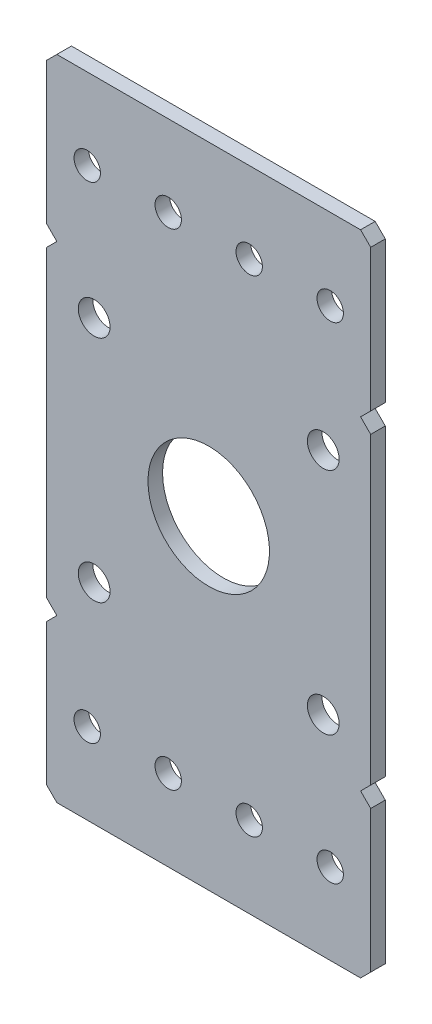
SolidWorks part; units mm, degrees
ref_plane "Front Plane" through (0, 0, 0) normal (0, 0, 1) x (1, 0, 0)
ref_plane "Top Plane" through (0, 0, 0) normal (0, 1, 0) x (1, 0, 0)
ref_plane "Right Plane" through (0, 0, 0) normal (1, 0, 0) x (0, 0, -1)
ref_plane "Plane1" through (0, 0, 2.286) normal (0, 0, 1) x (1, 0, 0)
sketch "Sketch1" plane through (0, 0, 2.286) normal (0, 0, 1) x (1, 0, 0)
  line L0 (25.4, -26.9875) -> (23.8125, -25.4)
  line L1 (23.8125, -25.4) -> (25.4, -23.8125)
  line L2 (25.4, -23.8125) -> (25.4, 23.8125)
  line L3 (25.4, 23.8125) -> (23.8125, 25.4)
  line L4 (23.8125, 25.4) -> (25.4, 26.9875)
  line L5 (25.4, 26.9875) -> (25.4, 49.2125)
  line L6 (25.4, 49.2125) -> (23.8125, 50.8)
  line L7 (23.8125, 50.8) -> (-23.8125, 50.8)
  line L8 (-23.8125, 50.8) -> (-25.4, 49.2125)
  line L9 (-25.4, 49.2125) -> (-25.4, 26.9875)
  line L10 (-25.4, 26.9875) -> (-23.8125, 25.4)
  line L11 (-23.8125, 25.4) -> (-25.4, 23.8125)
  line L12 (-25.4, 23.8125) -> (-25.4, -23.8125)
  line L13 (-25.4, -23.8125) -> (-23.8125, -25.4)
  line L14 (-23.8125, -25.4) -> (-25.4, -26.9875)
  line L15 (-25.4, -26.9875) -> (-25.4, -49.2125)
  line L16 (-25.4, -49.2125) -> (-23.8125, -50.8)
  line L17 (-23.8125, -50.8) -> (23.8125, -50.8)
  line L18 (23.8125, -50.8) -> (25.4, -49.2125)
  line L19 (25.4, -49.2125) -> (25.4, -26.9875)
  circle A0 centre (-17.9605, -17.9605) radius 2.4892
  circle A1 centre (-19.05, -38.1) radius 2.0701
  circle A2 centre (-6.35, -38.1) radius 2.0701
  circle A3 centre (19.05, -38.1) radius 2.0701
  circle A4 centre (0, 0) radius 9.525
  circle A5 centre (6.35, 38.1) radius 2.0701
  circle A6 centre (-19.05, 38.1) radius 2.0701
  circle A7 centre (-6.35, 38.1) radius 2.0701
  circle A8 centre (19.05, 38.1) radius 2.0701
  circle A9 centre (-17.9605, 17.9605) radius 2.4892
  circle A10 centre (6.35, -38.1) radius 2.0701
  circle A11 centre (17.9605, -17.9605) radius 2.4892
  circle A12 centre (17.9605, 17.9605) radius 2.4892
extrude "Boss-Extrude1" add sketch "Sketch1" against normal blind 2.286
